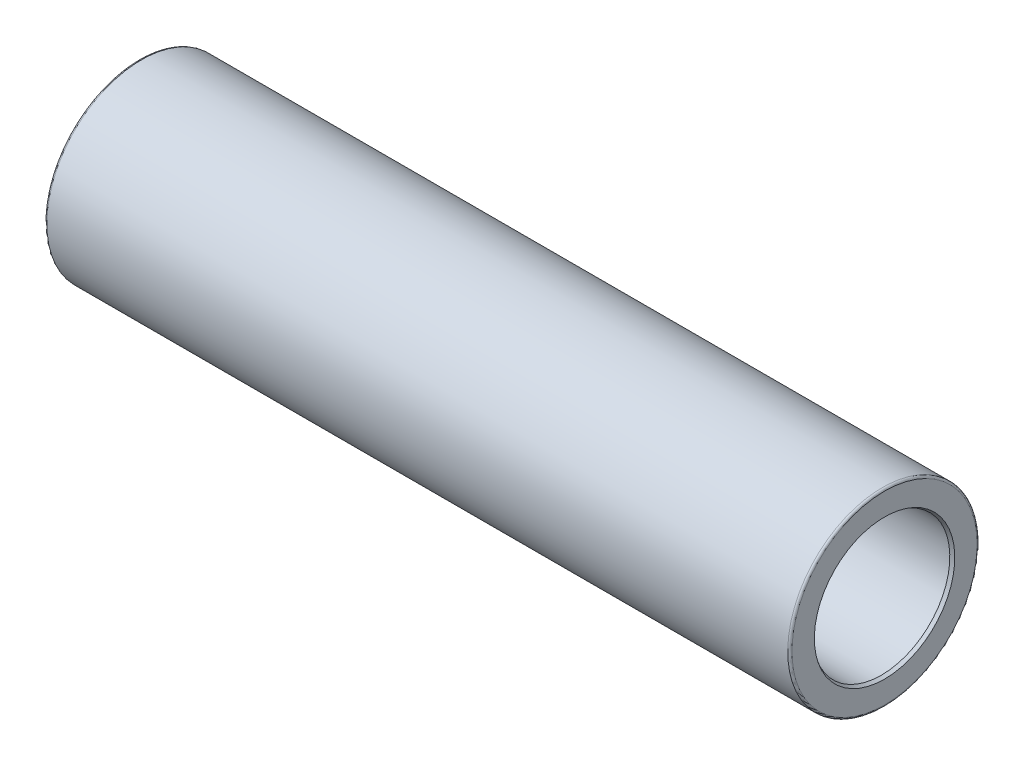
SolidWorks part; units mm, degrees
ref_plane "Plane1" through (0, 0, 0) normal (0, 0, 1) x (1, 0, 0)
ref_plane "Plane2" through (0, 0, 0) normal (0, 1, 0) x (1, 0, 0)
ref_plane "Plane3" through (0, 0, 0) normal (1, 0, 0) x (0, 0, -1)
sketch "Sketch1" plane through (0, 0, 0) normal (0, 0, 1) x (1, 0, 0)
  line L0 (-177, 0) -> (177, 0) construction
  line L1 (0, 93.3) -> (0, -101.2) construction
  line L2 (-177, 32.5) -> (-177, 44)
  line L3 (-176, 45) -> (176, 45)
  line L5 (-177, 32.5) -> (-120.4626, 32.5)
  line L6 (-120.4626, 32.5) -> (-118.5, 33.5)
  line L7 (-118.5, 33.5) -> (-116.5, 33.5)
  line L8 (-116.5, 33.5) -> (-116.5, 31.5)
  line L9 (-116.5, 31.5) -> (-107.1763, 31.5)
  line L10 (116.5, 33.5) -> (116.5, 31.5)
  line L11 (118.5, 33.5) -> (116.5, 33.5)
  line L12 (120.4626, 32.5) -> (118.5, 33.5)
  line L13 (177, 32.5) -> (120.4626, 32.5)
  line L15 (177, 32.5) -> (177, 44)
  line L16 (-106.8343, 31.5603) -> (-100.297, 33.9397)
  line L17 (-99.955, 34) -> (99.955, 34)
  line L18 (106.8343, 31.5603) -> (100.297, 33.9397)
  line L19 (107.1763, 31.5) -> (116.5, 31.5)
  arc A0 (-99.955, 34) -> (-100.297, 33.9397) centre (-99.955, 33) ccw
  arc A1 (-107.1763, 31.5) -> (-106.8343, 31.5603) centre (-107.1763, 32.5) ccw
  arc A2 (99.955, 34) -> (100.297, 33.9397) centre (99.955, 33) cw
  arc A3 (107.1763, 31.5) -> (106.8343, 31.5603) centre (107.1763, 32.5) cw
  arc A4 (-176, 45) -> (-177, 44) centre (-176, 44) ccw
  arc A5 (176, 45) -> (177, 44) centre (176, 44) cw
  point P23 (0, 45)
  point P26 (0, 34)
  point P28 (-100.1313, 34)
  point P31 (-107, 31.5)
  point P34 (100.1313, 34)
  point P37 (107, 31.5)
  point P40 (-177, 45)
  point P43 (177, 45)
  dimension "D14" = 1
  dimension "D15" = 1
  dimension "D1" = 354
  dimension "D2" = 90
  dimension "D4" = 27
  dimension "D5" = 60.5
  dimension "D6" = 65
  dimension "D7" = 68
  dimension "D9" = 2
  dimension "D10" = 67
  dimension "D11" = 63
  dimension "D12" = 20
  dimension "D13" = 70
revolve "Base-Revolve" add sketch "Sketch1" angle 360 about L0
sketch "Sketch5" plane through (0, 0, 0) normal (0, 0, 1) x (1, 0, 0)
  line L0 (0, 0) -> (0, 45) construction
  line L1 (176, 45) -> (-176, 45) construction
  line L2 (0, 0) -> (176, 0) construction
  line L3 (176, -45) -> (176, 45) construction
  line L4 (177, -44) -> (177, 44) construction
  line L5 (177, 32.5) -> (120.4626, 32.5) construction
  line L6 (177, 32.5) -> (177, 33.366)
  line L7 (177, 32.5) -> (175.5, 32.5)
  line L8 (175.5, 32.5) -> (177, 33.366)
  line L9 (-175.5, 32.5) -> (-177, 33.366)
  line L10 (-177, 32.5) -> (-175.5, 32.5)
  line L11 (-177, 32.5) -> (-177, 33.366)
  dimension "D1" = 1.5
  dimension "D2" = 30
revolve "2.5 x 30 gr reifning" cut sketch "Sketch5" angle 360 about L2
sketch "Sketch4" plane through (0, 0, 0) normal (1, 0, 0) x (0, 0, -1)
  line L1 (0, 0) -> (45, 0) construction
  line L2 (45, 0) -> (45, 10)
  line L3 (45, 10) -> (43, 10)
  line L4 (43, 10) -> (39.6352, 4.4)
  line L5 (39.6352, 4.4) -> (15, 4.4)
  line L6 (15, 4.4) -> (15, 0)
  line L7 (45, 0) -> (15, 0)
  line L8 (0, 0) -> (0, 45) construction
  circle A1 centre (0, 0) radius 45 construction
  circle A2 centre (0, 0) radius 45 construction
  dimension "D1" = 90
  dimension "D2" = 20
  dimension "D3" = 8.8
  dimension "D4" = 59
  dimension "D5" = 2
  dimension "D6" = 30
revolve "Udboring smørenippel" [suppressed] cut sketch "Sketch4" angle 360 about L1
cosmetic thread "Cosmetic Thread1" [suppressed] parameters "D2"=9.728
